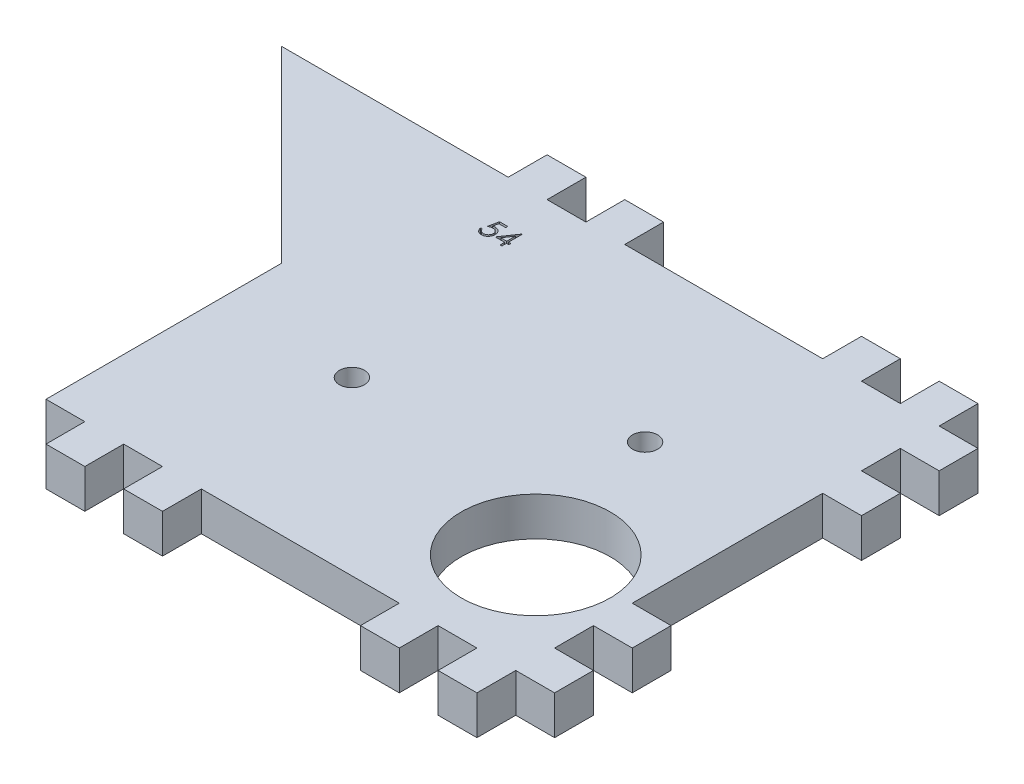
SolidWorks part; units mm, degrees
material "Acrylic (Medium-high impact)"
ref_plane "Front Plane" through (0, 0, 0) normal (0, 0, 1) x (1, 0, 0)
ref_plane "Top Plane" through (0, 0, 0) normal (0, 1, 0) x (1, 0, 0)
ref_plane "Right Plane" through (0, 0, 0) normal (1, 0, 0) x (0, 0, -1)
sketch "Sketch1" plane through (0, 0, 0) normal (0, 1, 0) x (1, 0, 0)
  line L0 (0, -6.2) -> (-30, -6.2)
  line L1 (0, 0) -> (81.2, 0)
  line L2 (0, 0) -> (0, -80)
  line L3 (0, -80) -> (81.2, -80)
  line L4 (81.2, 0) -> (81.2, -80)
  line L5 (0, 0) -> (6.2, 0)
  line L6 (0, 0) -> (0, -6.2)
  line L7 (0, -6.2) -> (6.2, -6.2)
  line L8 (6.2, 0) -> (6.2, -6.2)
  line L9 (12.4, 0) -> (18.6, 0)
  line L10 (12.4, 0) -> (12.4, -6.2)
  line L11 (12.4, -6.2) -> (18.6, -6.2)
  line L12 (18.6, 0) -> (18.6, -6.2)
  line L13 (81.2, 0) -> (75, 0)
  line L14 (81.2, 0) -> (81.2, -6.2)
  line L15 (81.2, -6.2) -> (75, -6.2)
  line L16 (75, 0) -> (75, -6.2)
  line L17 (68.8, 0) -> (62.6, 0)
  line L18 (68.8, 0) -> (68.8, -6.2)
  line L19 (68.8, -6.2) -> (62.6, -6.2)
  line L20 (62.6, 0) -> (62.6, -6.2)
  line L21 (56.4, 0) -> (24.8, 0)
  line L22 (56.4, 0) -> (56.4, -6.2)
  line L23 (56.4, -6.2) -> (24.8, -6.2)
  line L24 (24.8, 0) -> (24.8, -6.2)
  line L25 (81.2, -12.4) -> (75, -12.4)
  line L26 (81.2, -12.4) -> (81.2, -18.6)
  line L27 (81.2, -18.6) -> (75, -18.6)
  line L28 (75, -12.4) -> (75, -18.6)
  line L33 (81.2, -24.8) -> (75, -24.8)
  line L34 (81.2, -24.8) -> (81.2, -55.2)
  line L35 (81.2, -55.2) -> (75, -55.2)
  line L36 (75, -24.8) -> (75, -55.2)
  line L37 (81.2, -73.8) -> (75, -73.8)
  line L38 (81.2, -73.8) -> (81.2, -80)
  line L39 (81.2, -80) -> (75, -80)
  line L40 (75, -73.8) -> (75, -80)
  line L41 (81.2, -67.6) -> (75, -67.6)
  line L42 (81.2, -67.6) -> (81.2, -61.4)
  line L43 (81.2, -61.4) -> (75, -61.4)
  line L44 (75, -67.6) -> (75, -61.4)
  line L49 (68.8, -73.8) -> (62.6, -73.8)
  line L50 (68.8, -73.8) -> (68.8, -80)
  line L51 (68.8, -80) -> (62.6, -80)
  line L52 (62.6, -73.8) -> (62.6, -80)
  line L57 (56.4, -73.8) -> (24.8, -73.8)
  line L58 (56.4, -73.8) -> (56.4, -80)
  line L59 (56.4, -80) -> (24.8, -80)
  line L60 (24.8, -73.8) -> (24.8, -80)
  line L61 (0, -73.8) -> (6.2, -73.8)
  line L62 (0, -73.8) -> (0, -80)
  line L63 (0, -80) -> (6.2, -80)
  line L64 (6.2, -73.8) -> (6.2, -80)
  line L65 (12.4, -73.8) -> (18.6, -73.8)
  line L66 (12.4, -73.8) -> (12.4, -80)
  line L67 (12.4, -80) -> (18.6, -80)
  line L68 (18.6, -73.8) -> (18.6, -80)
  line L69 (-30, -6.2) -> (0, -36.2)
  circle A0 centre (60.62, -56.23) radius 11.9
  circle A1 centre (21.4188, -46.3768) radius 2
  circle A4 centre (53.7443, -31.8948) radius 2
  point P23 (60.62, -56.23)
  point P56 (21.4188, -46.3768)
  point P58 (53.7443, -31.8948)
  dimension "D16" = 6.2
  dimension "D17" = 6.2
  dimension "D1" = 81.2
  dimension "D2" = 80
  dimension "D3" = 6.2
  dimension "D4" = 6.2
  dimension "D5" = 6.2
  dimension "D6" = 6.2
  dimension "D7" = 6.2
  dimension "D8" = 6.2
  dimension "D9" = 6.2
  dimension "D10" = 6.2
  dimension "D11" = 6.2
  dimension "D12" = 6.2
  dimension "D13" = 6.2
  dimension "D14" = 6.2
  dimension "D15" = 6.2
  dimension "D18" = 6.2
  dimension "D19" = 6.2
  dimension "D20" = 6.2
  dimension "D21" = 6.2
  dimension "D22" = 21.4188
  dimension "D23" = 6.2
  dimension "D24" = 33.6232
  dimension "D25" = 6.2
  dimension "D26" = 30
  dimension "D30" = 6.2
extrude "Boss-Extrude1" add sketch "Sketch1" along normal blind 6.2 contours L65 L68 L3 L60 L57 L58 L52 L49 L50 L40 L37 L4 L41 L44 L43 L35 L36 L33 L27 L28 L25 L15 L16 L1 L18 L19 L20 L22 L23 L24 L12 L11 L10 L8 L7 L2 L61 L64 L66 A4 | L0 L69 L2
sketch "Sketch2" plane through (0, 6.2, 0) normal (0, 1, 0) x (1, 0, 0)
  text T0 "54"
extrude "Cut-Extrude1" cut sketch "Sketch2" against normal blind 1
